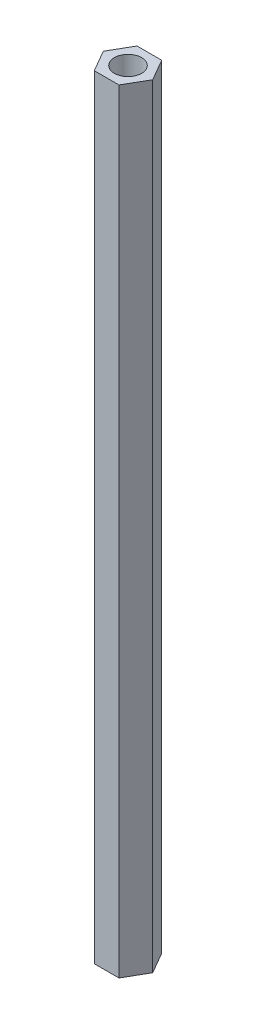
SolidWorks part; units mm, degrees
ref_plane "Front Plane" through (0, 0, 0) normal (0, 0, 1) x (1, 0, 0)
ref_plane "Top Plane" through (0, 0, 0) normal (0, 1, 0) x (1, 0, 0)
ref_plane "Right Plane" through (0, 0, 0) normal (1, 0, 0) x (0, 0, -1)
sketch "Sketch2" plane through (0, 0, 0) normal (0, 1, 0) x (1, 0, 0)
  line L1 (2.7135, 0) -> (1.3568, 2.35)
  line L2 (1.3568, 2.35) -> (-1.3568, 2.35)
  line L3 (-1.3568, 2.35) -> (-2.7135, 0)
  line L4 (-2.7135, 0) -> (-1.3568, -2.35)
  line L5 (-1.3568, -2.35) -> (1.3568, -2.35)
  line L6 (1.3568, -2.35) -> (2.7135, 0)
  circle A0 centre (0, 0) radius 2.35 construction
  circle A1 centre (0, 0) radius 1.5
  dimension "D1" = 4.7
  dimension "D3" = 3
  dimension "D2" = 2.35
extrude "Boss-Extrude1" add sketch "Sketch2" along normal blind 85
